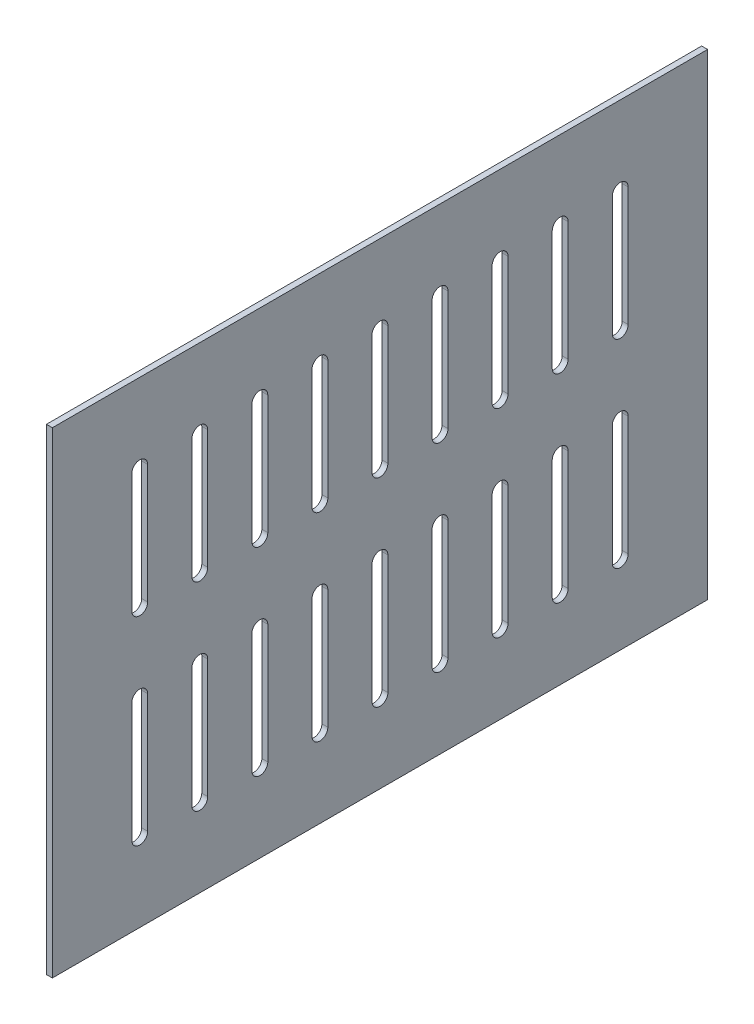
SolidWorks part; units mm, degrees
ref_plane "Ön Düzlem" through (0, 0, 0) normal (0, 0, 1) x (1, 0, 0)
ref_plane "Üst Düzlem" through (0, 0, 0) normal (0, 1, 0) x (1, 0, 0)
ref_plane "Sağ Düzlem" through (0, 0, 0) normal (1, 0, 0) x (0, 0, -1)
sketch "Çizim1" plane through (0, 0, 0) normal (1, 0, 0) x (0, 0, -1)
  line L0 (44, -40) -> (44, -100) construction
  line L1 (0, 0) -> (330, 0)
  line L2 (0, 0) -> (0, -240)
  line L3 (0, -240) -> (330, -240)
  line L4 (330, 0) -> (330, -240)
  line L5 (48, -40) -> (48, -100)
  line L6 (40, -40) -> (40, -100)
  line L7 (74.25, -40) -> (74.25, -100) construction
  line L8 (78.25, -40) -> (78.25, -100)
  line L9 (70.25, -40) -> (70.25, -100)
  line L10 (104.5, -40) -> (104.5, -100) construction
  line L11 (108.5, -40) -> (108.5, -100)
  line L12 (100.5, -40) -> (100.5, -100)
  line L13 (134.75, -40) -> (134.75, -100) construction
  line L14 (138.75, -40) -> (138.75, -100)
  line L15 (130.75, -40) -> (130.75, -100)
  line L16 (165, -40) -> (165, -100) construction
  line L17 (169, -40) -> (169, -100)
  line L18 (161, -40) -> (161, -100)
  line L19 (195.25, -40) -> (195.25, -100) construction
  line L20 (199.25, -40) -> (199.25, -100)
  line L21 (191.25, -40) -> (191.25, -100)
  line L22 (225.5, -40) -> (225.5, -100) construction
  line L23 (229.5, -40) -> (229.5, -100)
  line L24 (221.5, -40) -> (221.5, -100)
  line L25 (255.75, -40) -> (255.75, -100) construction
  line L26 (259.75, -40) -> (259.75, -100)
  line L27 (251.75, -40) -> (251.75, -100)
  line L28 (286, -40) -> (286, -100) construction
  line L29 (290, -40) -> (290, -100)
  line L30 (282, -40) -> (282, -100)
  line L31 (74.25, -140) -> (74.25, -200) construction
  line L32 (78.25, -140) -> (78.25, -200)
  line L33 (70.25, -140) -> (70.25, -200)
  line L34 (104.5, -140) -> (104.5, -200) construction
  line L35 (108.5, -140) -> (108.5, -200)
  line L36 (100.5, -140) -> (100.5, -200)
  line L37 (134.75, -140) -> (134.75, -200) construction
  line L38 (138.75, -140) -> (138.75, -200)
  line L39 (130.75, -140) -> (130.75, -200)
  line L40 (165, -140) -> (165, -200) construction
  line L41 (169, -140) -> (169, -200)
  line L42 (161, -140) -> (161, -200)
  line L43 (195.25, -140) -> (195.25, -200) construction
  line L44 (199.25, -140) -> (199.25, -200)
  line L45 (191.25, -140) -> (191.25, -200)
  line L46 (225.5, -140) -> (225.5, -200) construction
  line L47 (229.5, -140) -> (229.5, -200)
  line L48 (221.5, -140) -> (221.5, -200)
  line L49 (255.75, -140) -> (255.75, -200) construction
  line L50 (259.75, -140) -> (259.75, -200)
  line L51 (251.75, -140) -> (251.75, -200)
  line L52 (286, -140) -> (286, -200) construction
  line L53 (290, -140) -> (290, -200)
  line L54 (282, -140) -> (282, -200)
  line L55 (44, -140) -> (44, -200) construction
  line L56 (48, -140) -> (48, -200)
  line L57 (40, -140) -> (40, -200)
  arc A0 (48, -40) -> (40, -40) centre (44, -40) ccw
  arc A1 (40, -100) -> (48, -100) centre (44, -100) ccw
  arc A2 (78.25, -40) -> (70.25, -40) centre (74.25, -40) ccw
  arc A3 (70.25, -100) -> (78.25, -100) centre (74.25, -100) ccw
  arc A4 (108.5, -40) -> (100.5, -40) centre (104.5, -40) ccw
  arc A5 (100.5, -100) -> (108.5, -100) centre (104.5, -100) ccw
  arc A6 (138.75, -40) -> (130.75, -40) centre (134.75, -40) ccw
  arc A7 (130.75, -100) -> (138.75, -100) centre (134.75, -100) ccw
  arc A8 (169, -40) -> (161, -40) centre (165, -40) ccw
  arc A9 (161, -100) -> (169, -100) centre (165, -100) ccw
  arc A10 (199.25, -40) -> (191.25, -40) centre (195.25, -40) ccw
  arc A11 (191.25, -100) -> (199.25, -100) centre (195.25, -100) ccw
  arc A12 (229.5, -40) -> (221.5, -40) centre (225.5, -40) ccw
  arc A13 (221.5, -100) -> (229.5, -100) centre (225.5, -100) ccw
  arc A14 (259.75, -40) -> (251.75, -40) centre (255.75, -40) ccw
  arc A15 (251.75, -100) -> (259.75, -100) centre (255.75, -100) ccw
  arc A16 (290, -40) -> (282, -40) centre (286, -40) ccw
  arc A17 (282, -100) -> (290, -100) centre (286, -100) ccw
  arc A18 (78.25, -140) -> (70.25, -140) centre (74.25, -140) ccw
  arc A19 (70.25, -200) -> (78.25, -200) centre (74.25, -200) ccw
  arc A20 (108.5, -140) -> (100.5, -140) centre (104.5, -140) ccw
  arc A21 (100.5, -200) -> (108.5, -200) centre (104.5, -200) ccw
  arc A22 (138.75, -140) -> (130.75, -140) centre (134.75, -140) ccw
  arc A23 (130.75, -200) -> (138.75, -200) centre (134.75, -200) ccw
  arc A24 (169, -140) -> (161, -140) centre (165, -140) ccw
  arc A25 (161, -200) -> (169, -200) centre (165, -200) ccw
  arc A26 (199.25, -140) -> (191.25, -140) centre (195.25, -140) ccw
  arc A27 (191.25, -200) -> (199.25, -200) centre (195.25, -200) ccw
  arc A28 (229.5, -140) -> (221.5, -140) centre (225.5, -140) ccw
  arc A29 (221.5, -200) -> (229.5, -200) centre (225.5, -200) ccw
  arc A30 (259.75, -140) -> (251.75, -140) centre (255.75, -140) ccw
  arc A31 (251.75, -200) -> (259.75, -200) centre (255.75, -200) ccw
  arc A32 (290, -140) -> (282, -140) centre (286, -140) ccw
  arc A33 (282, -200) -> (290, -200) centre (286, -200) ccw
  arc A34 (48, -140) -> (40, -140) centre (44, -140) ccw
  arc A35 (40, -200) -> (48, -200) centre (44, -200) ccw
  point P7 (44, -70)
  point P16 (74.25, -70)
  point P23 (104.5, -70)
  point P30 (134.75, -70)
  point P37 (165, -70)
  point P44 (195.25, -70)
  point P51 (225.5, -70)
  point P58 (255.75, -70)
  point P65 (286, -70)
  point P72 (74.25, -170)
  point P79 (104.5, -170)
  point P86 (134.75, -170)
  point P93 (165, -170)
  point P100 (195.25, -170)
  point P107 (225.5, -170)
  point P114 (255.75, -170)
  point P121 (286, -170)
  point P128 (44, -170)
  dimension "D10" = 40
  dimension "D1" = 330
  dimension "D2" = 240
  dimension "D3" = 8
  dimension "D4" = 60
  dimension "D5" = 40
  dimension "D6" = 40
  dimension "D9" = 40
  dimension "D11" = 40
  dimension "D7" = 9
  dimension "D8" = 2
extrude "Yükseklik-Ekstrüzyon1" add sketch "Çizim1" along normal blind 3
